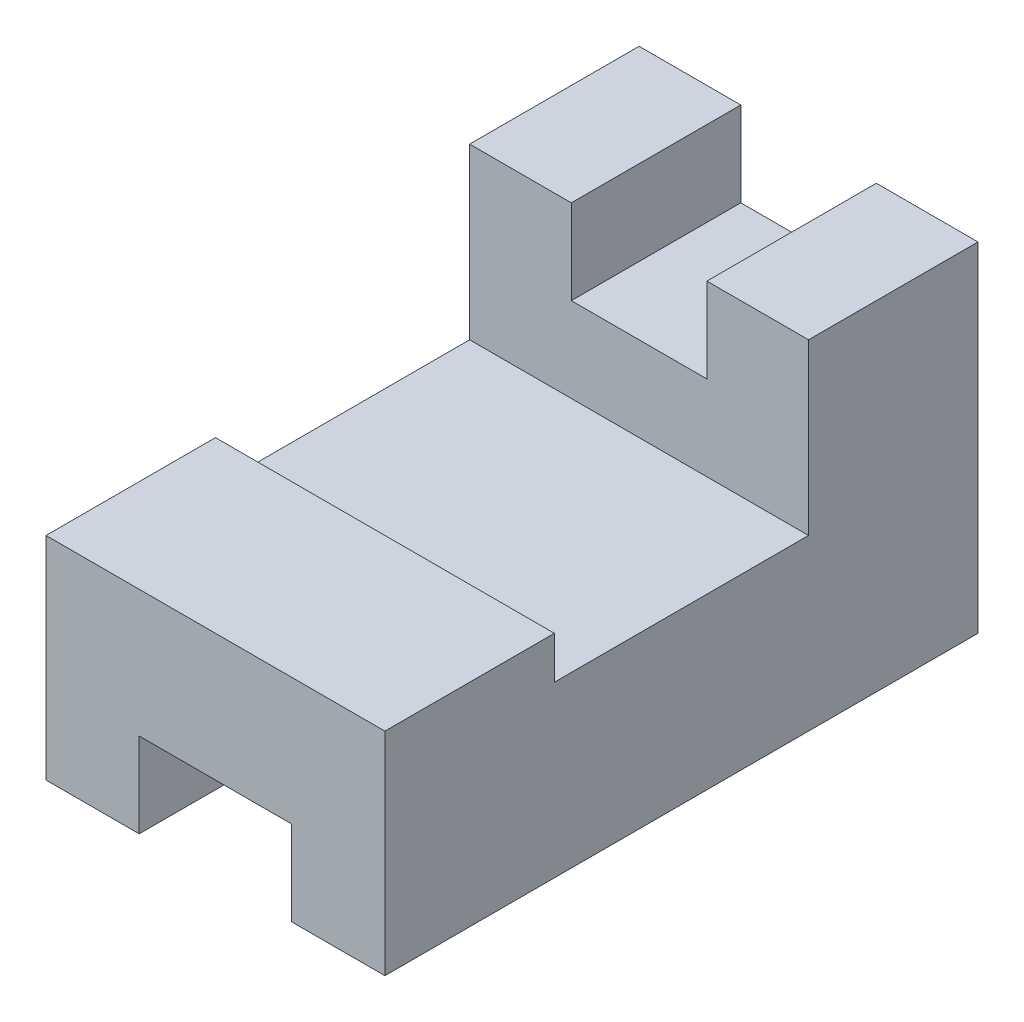
SolidWorks part; units mm, degrees
ref_plane "Ön Düzlem" through (0, 0, 0) normal (0, 0, 1) x (1, 0, 0)
ref_plane "Üst Düzlem" through (0, 0, 0) normal (0, 1, 0) x (1, 0, 0)
ref_plane "Sağ Düzlem" through (0, 0, 0) normal (1, 0, 0) x (0, 0, -1)
sketch "Çizim1" plane through (0, 0, 0) normal (0, 1, 0) x (1, 0, 0)
  line L1 (-20, 35) -> (20, 35)
  line L2 (-20, 35) -> (-20, -35)
  line L3 (-20, -35) -> (20, -35)
  line L4 (20, 35) -> (20, -35)
  line L5 (-20, 35) -> (20, -35) construction
  line L6 (-20, -35) -> (20, 35) construction
  point P0 (0, 0)
  dimension "D1" = 40
  dimension "D2" = 70
extrude "Yükseklik-Ekstrüzyon1" add sketch "Çizim1" along normal blind 20
sketch "Çizim2" plane through (0, 0, 35) normal (0, 0, 1) x (1, 0, 0)
  line L0 (-20, 0) -> (20, 0) construction
  line L1 (-9, 0) -> (9, 0)
  line L2 (-9, 0) -> (-9, 10)
  line L3 (-9, 10) -> (9, 10)
  line L4 (9, 0) -> (9, 10)
  point P6 (0, 10)
  dimension "D1" = 18
  dimension "D2" = 10
extrude "Kes-Ekstrüzyon1" cut sketch "Çizim2" against normal through all
sketch "Çizim3" plane through (0, 20, 0) normal (0, 1, 0) x (1, 0, 0)
  line L0 (20, -35) -> (20, 35) construction
  line L1 (-20, -35) -> (20, -35)
  line L2 (-20, -35) -> (-20, -15)
  line L3 (-20, -15) -> (20, -15)
  line L4 (20, -35) -> (20, -15)
  dimension "D1" = 20
extrude "Yükseklik-Ekstrüzyon2" add sketch "Çizim3" along normal blind 5
sketch "Çizim4" plane through (0, 20, 0) normal (0, 1, 0) x (1, 0, 0)
  line L0 (20, -15) -> (20, 35) construction
  line L1 (-20, 35) -> (20, 35)
  line L2 (-20, 35) -> (-20, 15)
  line L3 (-20, 15) -> (20, 15)
  line L4 (20, 35) -> (20, 15)
  dimension "D1" = 20
extrude "Yükseklik-Ekstrüzyon3" add sketch "Çizim4" along normal blind 20
sketch "Çizim5" plane through (0, 0, -15) normal (0, 0, 1) x (1, 0, 0)
  line L0 (-20, 40) -> (20, 40) construction
  line L1 (-8, 40) -> (8, 40)
  line L2 (-8, 40) -> (-8, 30)
  line L3 (-8, 30) -> (8, 30)
  line L4 (8, 40) -> (8, 30)
  point P6 (0, 30)
  dimension "D1" = 16
  dimension "D2" = 10
extrude "Kes-Ekstrüzyon2" cut sketch "Çizim5" against normal through all
